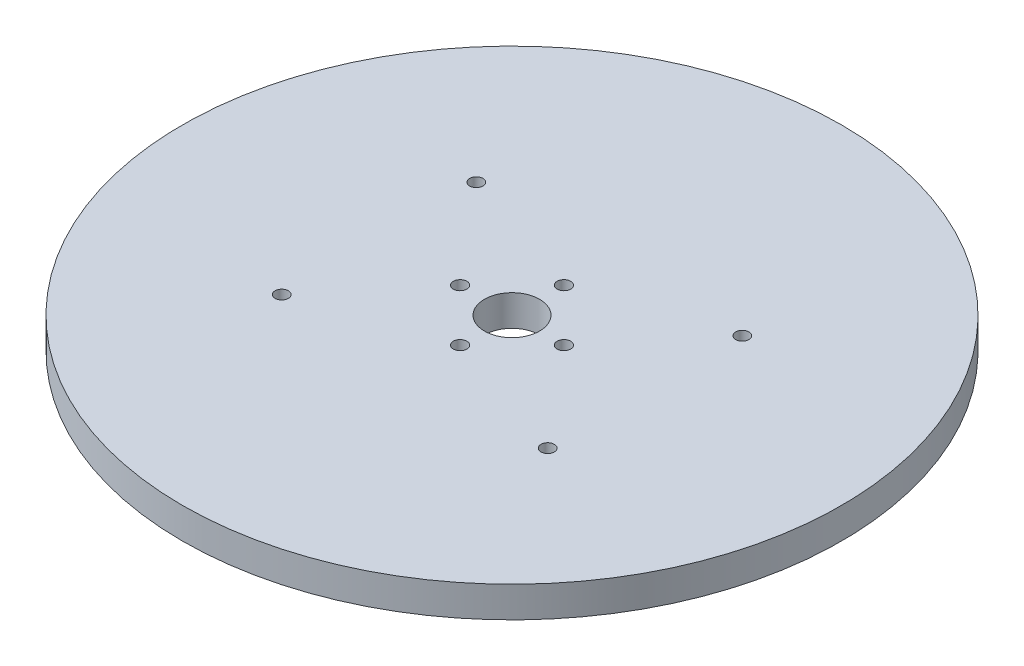
SolidWorks part; units mm, degrees
ref_plane "Front Plane" through (0, 0, 0) normal (0, 0, 1) x (1, 0, 0)
ref_plane "Top Plane" through (0, 0, 0) normal (0, 1, 0) x (1, 0, 0)
ref_plane "Right Plane" through (0, 0, 0) normal (1, 0, 0) x (0, 0, -1)
sketch "Sketch1" plane through (0, 0, 0) normal (0, 1, 0) x (1, 0, 0)
  circle A0 centre (0, 0) radius 50.8
  dimension "D1" = 101.6
extrude "Boss-Extrude1" add sketch "Sketch1" along normal blind 4.7625
sketch "Sketch2" plane through (0, 4.7625, 0) normal (0, 1, 0) x (-1, 0, 0)
  line L0 (8, 0) -> (-8, 0) construction
  line L1 (0, 8) -> (0, -8) construction
  circle A0 centre (0, 8) radius 1.05
  circle A1 centre (-8, 0) radius 1.05
  circle A2 centre (0, -8) radius 1.05
  circle A3 centre (8, 0) radius 1.05
  dimension "D1" = 2.1
  dimension "D2" = 16
extrude "Cut-Extrude1" cut sketch "Sketch2" against normal through all
sketch "Sketch3" plane through (0, 4.7625, 0) normal (0, 1, 0) x (-1, 0, 0)
  circle A0 centre (0, 0) radius 4.25
  dimension "D1" = 8.5
extrude "Cut-Extrude2" cut sketch "Sketch3" against normal through all
sketch "Sketch4" plane through (0, 4.7625, 0) normal (0, 1, 0) x (-1, 0, 0)
  line L1 (-20.5, -15) -> (20.5, -15) construction
  line L2 (-20.5, -15) -> (-20.5, 15) construction
  line L3 (-20.5, 15) -> (20.5, 15) construction
  line L4 (20.5, -15) -> (20.5, 15) construction
  line L5 (-20.5, -15) -> (20.5, 15) construction
  line L6 (-20.5, 15) -> (20.5, -15) construction
  circle A0 centre (-20.5, 15) radius 1.025
  circle A1 centre (20.5, 15) radius 1.025
  circle A2 centre (20.5, -15) radius 1.025
  circle A3 centre (-20.5, -15) radius 1.025
  point P0 (0, 0)
  dimension "D3" = 2.05
  dimension "D1" = 41
  dimension "D2" = 30
extrude "Cut-Extrude3" cut sketch "Sketch4" against normal through all
sketch "Sketch6" plane through (0, 0, 0) normal (0, -1, 0) x (1, 0, 0)
  line L1 (-20.5, -15) -> (20.5, -15) construction
  line L2 (-20.5, -15) -> (-20.5, 15) construction
  line L3 (-20.5, 15) -> (20.5, 15) construction
  line L4 (20.5, -15) -> (20.5, 15) construction
  line L5 (-20.5, -15) -> (20.5, 15) construction
  line L6 (-20.5, 15) -> (20.5, -15) construction
  line L7 (-17.6421, 15) -> (-19.0711, 17.475)
  line L8 (-19.0711, 17.475) -> (-21.9289, 17.475)
  line L9 (-21.9289, 17.475) -> (-23.3579, 15)
  line L10 (-23.3579, 15) -> (-21.9289, 12.525)
  line L11 (-21.9289, 12.525) -> (-19.0711, 12.525)
  line L12 (-19.0711, 12.525) -> (-17.6421, 15)
  line L13 (21.9289, 17.475) -> (19.0711, 17.475)
  line L14 (19.0711, 17.475) -> (17.6421, 15)
  line L15 (17.6421, 15) -> (19.0711, 12.525)
  line L16 (19.0711, 12.525) -> (21.9289, 12.525)
  line L17 (21.9289, 12.525) -> (23.3579, 15)
  line L18 (23.3579, 15) -> (21.9289, 17.475)
  line L19 (21.9289, -12.525) -> (19.0711, -12.525)
  line L20 (19.0711, -12.525) -> (17.6421, -15)
  line L21 (17.6421, -15) -> (19.0711, -17.475)
  line L22 (19.0711, -17.475) -> (21.9289, -17.475)
  line L23 (21.9289, -17.475) -> (23.3579, -15)
  line L24 (23.3579, -15) -> (21.9289, -12.525)
  line L25 (-21.9289, -12.525) -> (-23.3579, -15)
  line L26 (-23.3579, -15) -> (-21.9289, -17.475)
  line L27 (-21.9289, -17.475) -> (-19.0711, -17.475)
  line L28 (-19.0711, -17.475) -> (-17.6421, -15)
  line L29 (-17.6421, -15) -> (-19.0711, -12.525)
  line L30 (-19.0711, -12.525) -> (-21.9289, -12.525)
  circle A0 centre (0, 0) radius 15
  circle A1 centre (-20.5, 15) radius 2.475 construction
  circle A2 centre (20.5, 15) radius 2.475 construction
  circle A3 centre (20.5, -15) radius 2.475 construction
  circle A4 centre (-20.5, -15) radius 2.475 construction
  arc A5 (-13.1298, 16.3893) -> (-19.594, 7.5549) centre (-20.5, 15) ccw
  arc A6 (19.594, 7.5549) -> (13.1298, 16.3893) centre (20.5, 15) ccw
  arc A7 (-19.594, 7.5549) -> (-19.594, -7.5549) centre (0, 0) ccw
  arc A8 (-19.594, -7.5549) -> (-13.1298, -16.3893) centre (-20.5, -15) ccw
  arc A9 (13.1298, -16.3893) -> (19.594, -7.5549) centre (20.5, -15) ccw
  arc A10 (13.1298, 16.3893) -> (-13.1298, 16.3893) centre (0, 0) ccw
  arc A11 (19.594, -7.5549) -> (19.594, 7.5549) centre (0, 0) ccw
  arc A12 (-13.1298, -16.3893) -> (13.1298, -16.3893) centre (0, 0) ccw
  dimension "D2" = 30
  dimension "D3" = 15
  dimension "D4" = 6
  dimension "D1" = 4.95
extrude "Boss-Extrude2" add sketch "Sketch6" along normal blind 1.5875 separate body
sketch "Sketch7" [suppressed] plane through (0, -1.5875, 0) normal (0, -1, 0) x (1, 0, 0)
  line L0 (-19.0711, 12.525) -> (-17.6421, 15) construction
  line L1 (-17.6421, 15) -> (-19.0711, 17.475) construction
  line L2 (-19.0711, 17.475) -> (-21.9289, 17.475) construction
  line L3 (-21.9289, 17.475) -> (-23.3579, 15) construction
  line L4 (-23.3579, 15) -> (-21.9289, 12.525) construction
  line L5 (-21.9289, 12.525) -> (-19.0711, 12.525) construction
  line L6 (21.9289, 17.475) -> (19.0711, 17.475) construction
  line L7 (23.3579, 15) -> (21.9289, 17.475) construction
  line L8 (21.9289, 12.525) -> (23.3579, 15) construction
  line L9 (19.0711, 12.525) -> (21.9289, 12.525) construction
  line L10 (17.6421, 15) -> (19.0711, 12.525) construction
  line L11 (19.0711, 17.475) -> (17.6421, 15) construction
  line L12 (21.9289, -12.525) -> (19.0711, -12.525) construction
  line L13 (23.3579, -15) -> (21.9289, -12.525) construction
  line L14 (21.9289, -17.475) -> (23.3579, -15) construction
  line L15 (19.0711, -17.475) -> (21.9289, -17.475) construction
  line L16 (17.6421, -15) -> (19.0711, -17.475) construction
  line L17 (19.0711, -12.525) -> (17.6421, -15) construction
  line L18 (-19.0711, -12.525) -> (-21.9289, -12.525) construction
  line L19 (-17.6421, -15) -> (-19.0711, -12.525) construction
  line L20 (-19.0711, -17.475) -> (-17.6421, -15) construction
  line L21 (-21.9289, -17.475) -> (-19.0711, -17.475) construction
  line L22 (-23.3579, -15) -> (-21.9289, -17.475) construction
  line L23 (-21.9289, -12.525) -> (-23.3579, -15) construction
  line L24 (-19.0711, 12.525) -> (-17.6421, 15)
  line L25 (-17.6421, 15) -> (-19.0711, 17.475)
  line L26 (-19.0711, 17.475) -> (-21.9289, 17.475)
  line L27 (-21.9289, 17.475) -> (-23.3579, 15)
  line L28 (-23.3579, 15) -> (-21.9289, 12.525)
  line L29 (-21.9289, 12.525) -> (-19.0711, 12.525)
  line L30 (21.9289, 17.475) -> (19.0711, 17.475)
  line L31 (23.3579, 15) -> (21.9289, 17.475)
  line L32 (21.9289, 12.525) -> (23.3579, 15)
  line L33 (19.0711, 12.525) -> (21.9289, 12.525)
  line L34 (17.6421, 15) -> (19.0711, 12.525)
  line L35 (19.0711, 17.475) -> (17.6421, 15)
  line L36 (21.9289, -12.525) -> (19.0711, -12.525)
  line L37 (23.3579, -15) -> (21.9289, -12.525)
  line L38 (21.9289, -17.475) -> (23.3579, -15)
  line L39 (19.0711, -17.475) -> (21.9289, -17.475)
  line L40 (17.6421, -15) -> (19.0711, -17.475)
  line L41 (19.0711, -12.525) -> (17.6421, -15)
  line L42 (-19.0711, -12.525) -> (-21.9289, -12.525)
  line L43 (-17.6421, -15) -> (-19.0711, -12.525)
  line L44 (-19.0711, -17.475) -> (-17.6421, -15)
  line L45 (-21.9289, -17.475) -> (-19.0711, -17.475)
  line L46 (-23.3579, -15) -> (-21.9289, -17.475)
  line L47 (-21.9289, -12.525) -> (-23.3579, -15)
  circle A0 centre (0, 0) radius 15 construction
  circle A1 centre (0, 0) radius 15
  arc A8 (13.1298, 16.3893) -> (-13.1298, 16.3893) centre (0, 0) ccw
  arc A9 (-13.1298, 16.3893) -> (-19.594, 7.5549) centre (-20.5, 15) ccw
  arc A10 (-19.594, 7.5549) -> (-19.594, -7.5549) centre (0, 0) ccw
  arc A11 (-19.594, -7.5549) -> (-13.1298, -16.3893) centre (-20.5, -15) ccw
  arc A12 (-13.1298, -16.3893) -> (13.1298, -16.3893) centre (0, 0) ccw
  arc A13 (13.1298, -16.3893) -> (19.594, -7.5549) centre (20.5, -15) ccw
  arc A14 (19.594, -7.5549) -> (19.594, 7.5549) centre (0, 0) ccw
  arc A15 (19.594, 7.5549) -> (13.1298, 16.3893) centre (20.5, 15) ccw
  arc A16 (13.1298, 16.3893) -> (-13.1298, 16.3893) centre (0, 0) ccw
  arc A17 (-13.1298, 16.3893) -> (-19.594, 7.5549) centre (-20.5, 15) ccw
  arc A18 (-19.594, 7.5549) -> (-19.594, -7.5549) centre (0, 0) ccw
  arc A19 (-19.594, -7.5549) -> (-13.1298, -16.3893) centre (-20.5, -15) ccw
  arc A20 (-13.1298, -16.3893) -> (13.1298, -16.3893) centre (0, 0) ccw
  arc A21 (13.1298, -16.3893) -> (19.594, -7.5549) centre (20.5, -15) ccw
  arc A22 (19.594, -7.5549) -> (19.594, 7.5549) centre (0, 0) ccw
  arc A23 (19.594, 7.5549) -> (13.1298, 16.3893) centre (20.5, 15) ccw
  dimension "D1" = 0
sketch "Sketch8" plane through (0, 4.7625, 0) normal (0, 1, 0) x (1, 0, 0)
  circle A0 centre (-20.5, 15) radius 1.025 construction
  circle A1 centre (0, 0) radius 50.8
  circle A2 centre (0, 0) radius 50.8
  circle A3 centre (20.5, 15) radius 1.025 construction
  circle A4 centre (20.5, -15) radius 1.025 construction
  circle A5 centre (-20.5, -15) radius 1.025 construction
  circle A6 centre (0, 0) radius 4.25 construction
  circle A7 centre (-8, 0) radius 1.05 construction
  circle A8 centre (0, 8) radius 1.05 construction
  circle A9 centre (8, 0) radius 1.05 construction
  circle A10 centre (0, -8) radius 1.05 construction
  circle A11 centre (-20.5, 15) radius 1.025
  circle A12 centre (20.5, 15) radius 1.025
  circle A13 centre (20.5, -15) radius 1.025
  circle A14 centre (-20.5, -15) radius 1.025
  circle A15 centre (0, 0) radius 4.25
  circle A16 centre (-8, 0) radius 1.05
  circle A17 centre (0, 8) radius 1.05
  circle A18 centre (8, 0) radius 1.05
  circle A19 centre (0, -8) radius 1.05
  dimension "D1" = 0
